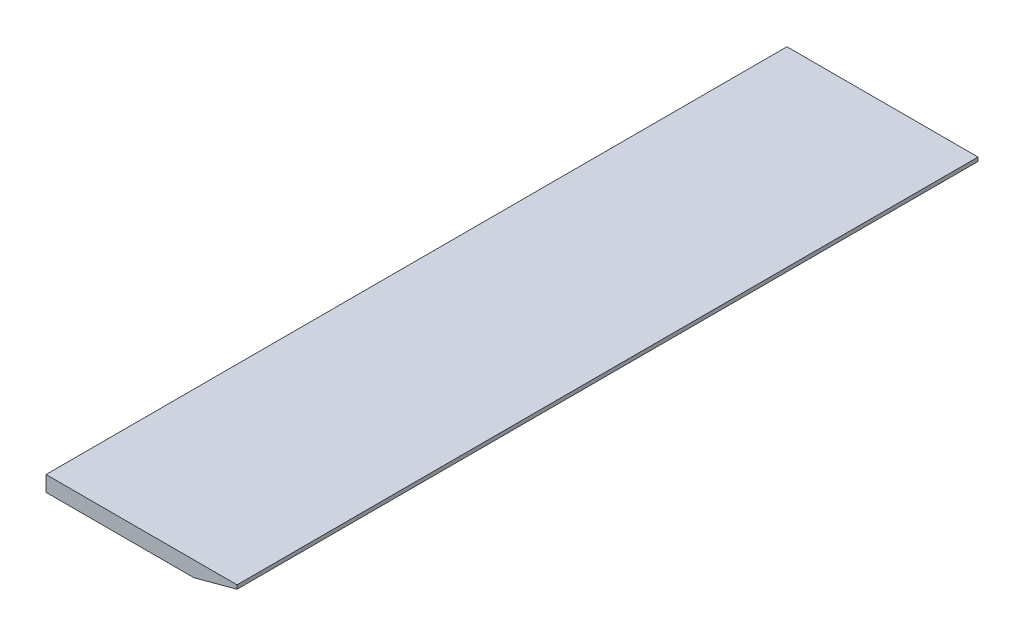
SolidWorks part; units mm, degrees
material "Pine"
ref_plane "Front Plane" through (0, 0, 0) normal (0, 0, 1) x (1, 0, 0)
ref_plane "Top Plane" through (0, 0, 0) normal (0, 1, 0) x (1, 0, 0)
ref_plane "Right Plane" through (0, 0, 0) normal (1, 0, 0) x (0, 0, -1)
sketch "Sketch1" plane through (0, 0, 0) normal (0, 0, 1) x (1, 0, 0)
  line L0 (0, 0) -> (0, 12.7)
  line L1 (0, 12.7) -> (157.1752, 12.7)
  line L2 (157.1752, 12.7) -> (157.1752, 9.525)
  line L3 (157.1752, 9.525) -> (121.6274, 0)
  line L4 (121.6274, 0) -> (0, 0)
  dimension "D1" = 157.1752
  dimension "D2" = 3.175
  dimension "D3" = 12.7
  dimension "D4" = 15
extrude "Boss-Extrude1" add sketch "Sketch1" along normal mid plane 609.6
